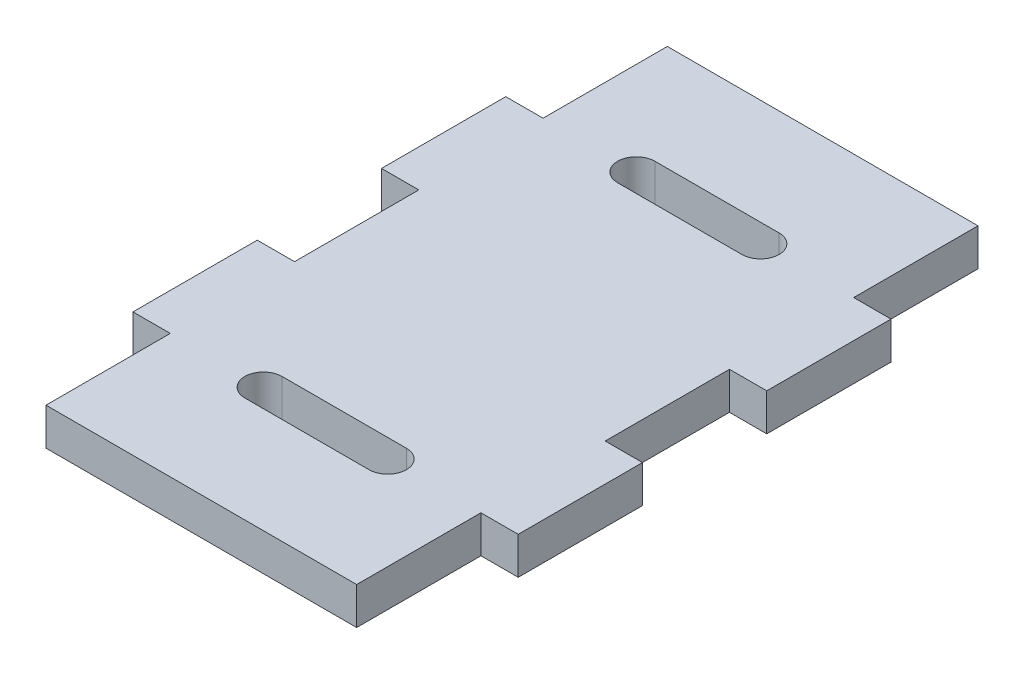
SolidWorks part; units mm, degrees
material "PC High Viscosity"
ref_plane "Front Plane" through (0, 0, 0) normal (0, 0, 1) x (1, 0, 0)
ref_plane "Top Plane" through (0, 0, 0) normal (0, 1, 0) x (1, 0, 0)
ref_plane "Right Plane" through (0, 0, 0) normal (1, 0, 0) x (0, 0, -1)
sketch "Sketch1" plane through (0, 0, 0) normal (0, 1, 0) x (1, 0, 0)
  line L0 (-12.5, 0) -> (12.5, 0) construction
  line L1 (12.5, -25) -> (-12.5, -25)
  line L2 (12.5, -25) -> (12.5, 25)
  line L3 (12.5, 25) -> (-12.5, 25)
  line L4 (-12.5, -25) -> (-12.5, 25)
  line L5 (12.5, -25) -> (-12.5, 25) construction
  line L6 (12.5, 25) -> (-12.5, -25) construction
  line L7 (-5, 15) -> (5, 15) construction
  line L8 (-5, 16.5) -> (5, 16.5)
  line L9 (-5, 13.5) -> (5, 13.5)
  line L10 (0, 25) -> (0, -25) construction
  line L11 (-5, -15) -> (5, -15) construction
  line L12 (-5, -16.5) -> (5, -16.5)
  line L13 (-5, -13.5) -> (5, -13.5)
  arc A0 (-5, 16.5) -> (-5, 13.5) centre (-5, 15) ccw
  arc A1 (5, 13.5) -> (5, 16.5) centre (5, 15) ccw
  arc A2 (-5, -16.5) -> (-5, -13.5) centre (-5, -15) cw
  arc A3 (5, -13.5) -> (5, -16.5) centre (5, -15) cw
  point P0 (0, 0)
  point P10 (0, 15)
  point P19 (0, -15)
  dimension "D1" = 25
  dimension "D2" = 50
  dimension "D3" = 3
  dimension "D4" = 10
  dimension "D5" = 15
extrude "Boss-Extrude1" add sketch "Sketch1" along normal blind 3
sketch "Sketch2" plane through (0, 3, 0) normal (0, 1, 0) x (1, 0, 0)
  line L0 (12.5, -25) -> (12.5, 25) construction
  line L1 (12.5, 15) -> (15.5, 15)
  line L2 (12.5, 15) -> (12.5, 5)
  line L3 (12.5, 5) -> (15.5, 5)
  line L4 (15.5, 15) -> (15.5, 5)
  line L5 (12.5, 0) -> (-12.5, 0) construction
  line L6 (12.5, -5) -> (15.5, -5)
  line L7 (12.5, -5) -> (12.5, -15)
  line L8 (12.5, -15) -> (15.5, -15)
  line L9 (15.5, -5) -> (15.5, -15)
  line L10 (-12.5, 25) -> (-12.5, -25) construction
  line L11 (0, 25) -> (0, -25) construction
  line L12 (12.5, 25) -> (-12.5, 25) construction
  line L13 (-12.5, -25) -> (12.5, -25) construction
  line L14 (12.5, 5) -> (12.5, -5) construction
  line L15 (-15.5, -5) -> (-15.5, -15)
  line L16 (-12.5, -15) -> (-15.5, -15)
  line L17 (-12.5, -5) -> (-12.5, -15)
  line L18 (-12.5, -5) -> (-15.5, -5)
  line L19 (-15.5, 15) -> (-15.5, 5)
  line L20 (-12.5, 5) -> (-15.5, 5)
  line L21 (-12.5, 15) -> (-12.5, 5)
  line L22 (-12.5, 15) -> (-15.5, 15)
  dimension "D1" = 10
  dimension "D2" = 3
extrude "Boss-Extrude2" add sketch "Sketch2" against normal up to surface (3 mm away) up to face at (0, 0, -15)
equation "\"pulley_pitch_diam\"= 12.73mm"
equation "\"pulley_total_width\"= 16mm"
equation "\"pulley_total_diam\"= 16mm"
equation "\"belt_width\"= 6mm"
equation "\"material_thickness\"= 3mm"
equation "\"shaft_diam\"= 8mm"
equation "\"bearing_od\"= 22mm"
equation "\"bearing_thickness\"= 7mm"
